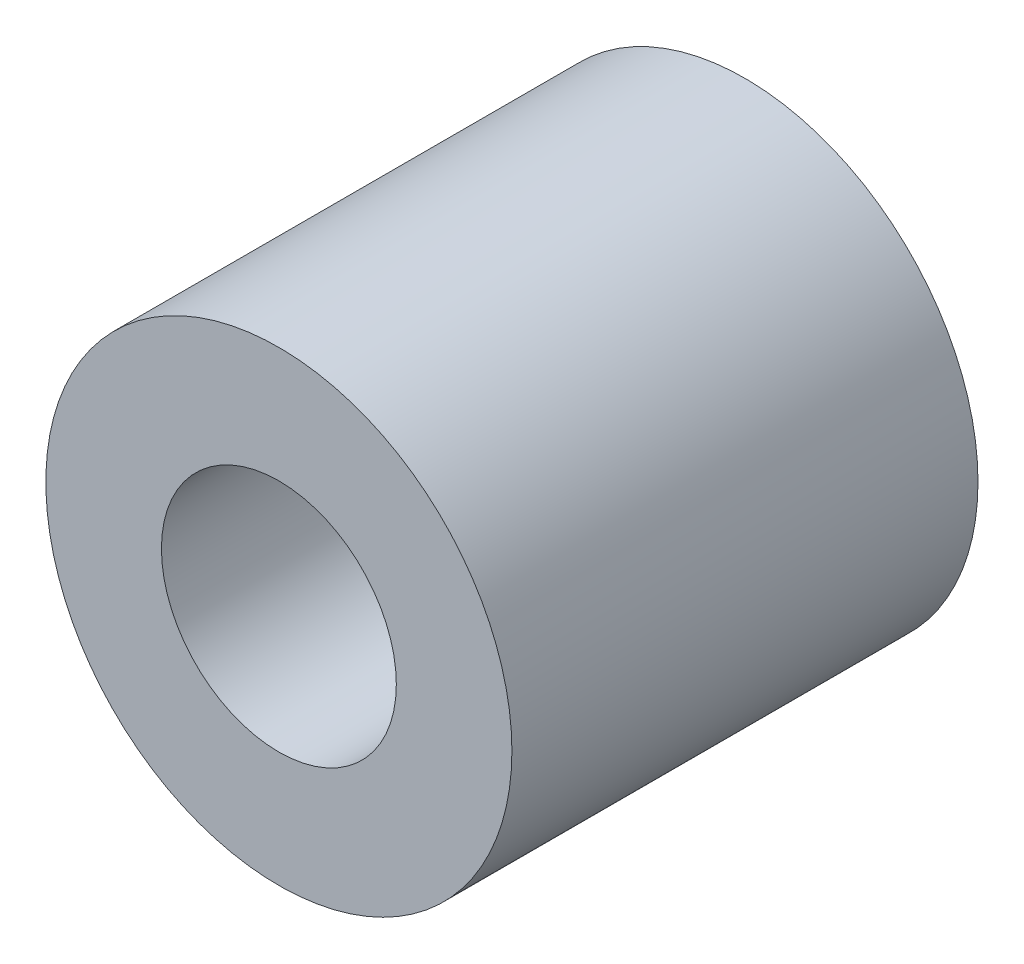
SolidWorks part; units mm, degrees
material "Nylon 101"
ref_plane "Front Plane" through (0, 0, 0) normal (0, 0, 1) x (1, 0, 0)
ref_plane "Top Plane" through (0, 0, 0) normal (0, 1, 0) x (1, 0, 0)
ref_plane "Right Plane" through (0, 0, 0) normal (1, 0, 0) x (0, 0, -1)
sketch "Sketch1" plane through (0, 0, 0) normal (0, 0, 1) x (1, 0, 0)
  line L0 (0, 3.2004) -> (0, 6.35) construction
  line L1 (0, -3.2004) -> (0, -6.35) construction
  circle A0 centre (0, 0) radius 6.35
  circle A1 centre (0, 0) radius 3.2004
  dimension "OD" = 12.7
  dimension "ID" = 6.4008
sketch "Sketch2" plane through (0, 0, 0) normal (1, 0, 0) x (0, 0, -1)
  line L0 (-6.35, 3.2004) -> (6.35, 3.2004) construction
  line L1 (-6.35, -3.2004) -> (6.35, -3.2004) construction
  line L2 (-6.35, -6.35) -> (6.35, -6.35) construction
  line L3 (-6.35, 6.35) -> (6.35, 6.35) construction
  dimension "Length" = 12.7
extrude "Extrude1" add sketch "Sketch1" along normal up to vertex (6.35 mm away) and the other way up to vertex (6.35 mm away) up to point (0, 3.2004, 6.35) other way up to point (0, 3.2004, -6.35)
sketch "Sketch3" plane through (0, 0, 6.35) normal (0, 0, 1) x (1, 0, 0)
  circle A0 centre (0, 0) radius 3.2004 construction
  circle A3 centre (0, 0) radius 3.2004
  point P3 (-3.2004, 0)
